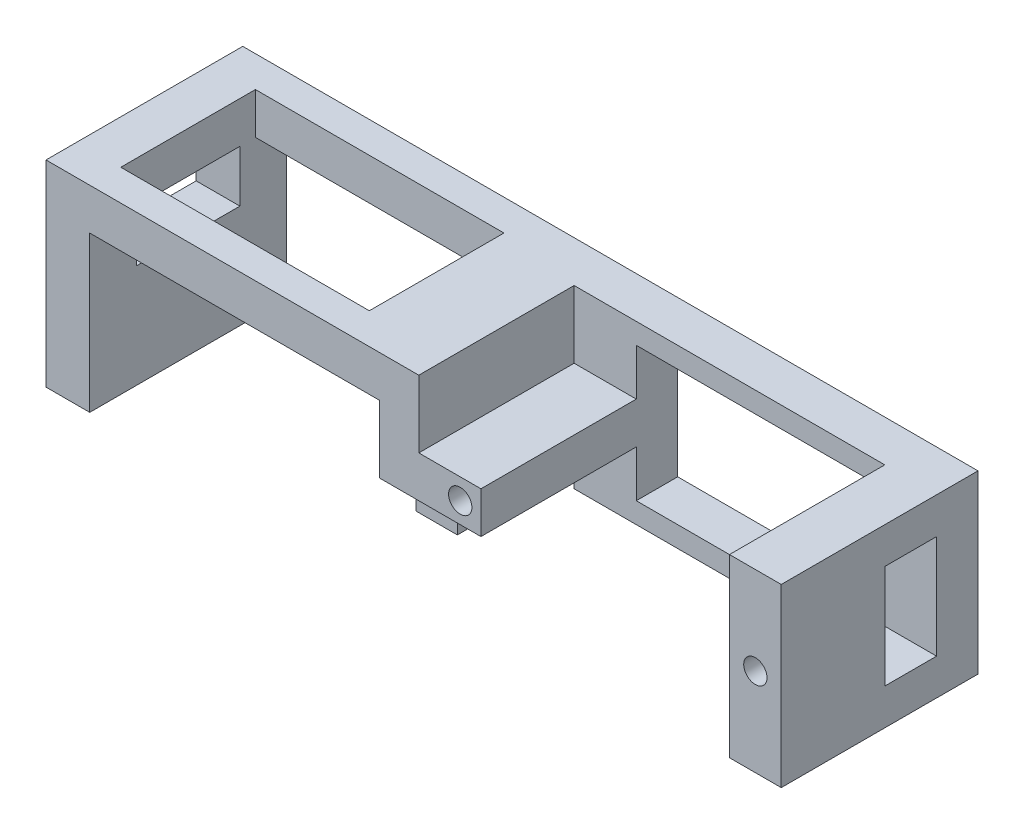
SolidWorks part; units mm, degrees
ref_plane "前基準面" through (0, 0, 0) normal (0, 0, 1) x (1, 0, 0)
ref_plane "上基準面" through (0, 0, 0) normal (0, 1, 0) x (1, 0, 0)
ref_plane "右基準面" through (0, 0, 0) normal (1, 0, 0) x (0, 0, -1)
sketch "草圖1" plane through (0, 0, 0) normal (0, 0, 1) x (1, 0, 0)
  line L0 (-21.2211, 2.8) -> (13.7789, 2.8) construction
  line L1 (-21.2211, 11.3) -> (13.7789, 11.3)
  line L2 (-21.2211, 11.3) -> (-21.2211, -5.7)
  line L3 (-21.2211, -5.7) -> (13.7789, -5.7)
  line L4 (13.7789, 11.3) -> (13.7789, -5.7)
  dimension "D1" = 35
  dimension "D2" = 8.5
extrude "填料-伸長1" add sketch "草圖1" along normal blind 4
sketch "草圖2" plane through (0, 0, 0) normal (0, 0, 1) x (1, 0, 0)
  line L0 (-21.2211, 2.8) -> (13.7789, 2.8) construction
  line L1 (-21.2211, 11.3) -> (-21.2211, -5.7) construction
  line L2 (13.7789, -5.7) -> (13.7789, 11.3) construction
  line L3 (-3.7211, 11.3) -> (-3.7211, -5.7) construction
  line L4 (13.7789, 11.3) -> (-21.2211, 11.3) construction
  line L5 (-21.2211, -5.7) -> (13.7789, -5.7) construction
  line L7 (-15.2211, 9.3) -> (8.7789, 9.3)
  line L8 (-15.2211, 9.3) -> (-15.2211, -3.7)
  line L9 (-15.2211, -3.7) -> (8.7789, -3.7)
  line L10 (8.7789, 9.3) -> (8.7789, -3.7)
  dimension "D1" = 24
  dimension "D2" = 13
  dimension "D3" = 6.5
  dimension "D4" = 5
extrude "除料-伸長1" cut sketch "草圖2" along normal blind 6
ref_plane "平面1" through (13.7789, 0, 0) normal (1, 0, 0) x (0, 0, -1)
sketch "草圖3" plane through (13.7789, 0, 0) normal (1, 0, 0) x (0, 0, -1)
  line L0 (-4, 2.8025) -> (-19, 2.8025) construction
  line L1 (-4, 11.3) -> (-19, 11.3)
  line L3 (-4, -5.6949) -> (-19, -5.6949)
  line L4 (-19, 11.3) -> (-19, -5.6949)
  line L5 (-4, 11.3) -> (-4, -5.6949)
  line L6 (-9, 7.8025) -> (-4, 7.8025)
  line L7 (-9, 7.8025) -> (-9, -2.1975)
  line L8 (-9, -2.1975) -> (-4, -2.1975)
  line L9 (-4, 7.8025) -> (-4, -2.1975)
  dimension "D1" = 15
  dimension "D2" = 5
  dimension "D3" = 10
  dimension "D4" = 5
extrude "填料-伸長2" add sketch "草圖3" against normal blind 5 contours L7 L0 L4 L3 L5 L8 | L0 L7 L6 L5 L1 L4
ref_plane "平面2" through (0, 0, 4) normal (0, 0, 1) x (1, 0, 0)
sketch "草圖5" plane through (0, 0, 4) normal (0, 0, 1) x (1, 0, 0)
  line L0 (-21.2211, 2.8) -> (-15.2211, 2.8) construction
  line L1 (-21.2211, 11.3) -> (-21.2211, -5.7) construction
  line L2 (-15.2211, -3.7) -> (-15.2211, 9.3) construction
  line L3 (-17.2211, 4.8) -> (-17.2211, 0.8) construction
  line L4 (-19.2211, 4.8) -> (-15.2211, 4.8)
  line L5 (-19.2211, 4.8) -> (-19.2211, 0.8)
  line L6 (-19.2211, 0.8) -> (-15.2211, 0.8)
  line L7 (-15.2211, 4.8) -> (-15.2211, 0.8)
  circle A0 centre (-17.2211, 2.8) radius 1.125
  dimension "D4" = 2.25
  dimension "D1" = 4
  dimension "D2" = 4
  dimension "D3" = 2
extrude "填料-伸長3" add sketch "草圖5" along normal blind 15
ref_plane "平面3" through (0, 0, 19) normal (0, 0, 1) x (1, 0, 0)
sketch "草圖6" plane through (0, 0, 19) normal (0, 0, 1) x (1, 0, 0)
  line L0 (8.7789, 2.8025) -> (13.7789, 2.8025) construction
  line L1 (8.7789, 11.3) -> (8.7789, -5.6949) construction
  line L2 (13.7789, -9.35) -> (13.7789, 9.35) construction
  line L3 (11.2789, 11.3) -> (11.2789, -5.6949) construction
  line L4 (8.7789, 11.3) -> (13.7789, 11.3) construction
  line L5 (8.7789, -5.6949) -> (13.7789, -5.6949) construction
  circle A0 centre (11.2789, 2.8025) radius 1.125
  dimension "D1" = 2.25
extrude "除料-伸長2" cut sketch "草圖6" against normal blind 15
ref_plane "平面4" through (-21.2211, 0, 0) normal (-1, 0, 0) x (0, 0, 1)
sketch "草圖7" plane through (-21.2211, 0, 0) normal (-1, 0, 0) x (0, 0, 1)
  line L6 (4, 4.8) -> (4, 0.7965)
  line L7 (4, -3.575) -> (4, 3.575) construction
  line L8 (19, 4.8) -> (4, 4.8) construction
  line L9 (4, 0.7965) -> (19, 0.8)
  line L10 (19, -2.75) -> (19, 2.75) construction
  line L11 (19, 0.8) -> (4, 0.8) construction
  line L12 (19, 0.8) -> (19, 4.8)
  line L13 (19, 4.8) -> (4, 4.8)
extrude "填料-伸長5" add sketch "草圖7" against normal blind 2
ref_plane "平面5" through (0, 3, 0) normal (0, 1, 0) x (1, 0, 0)
sketch "草圖8" plane through (0, 3, 0) normal (0, 1, 0) x (1, 0, 0)
  line L1 (-21.2211, -19) -> (-57.2211, -19)
  line L2 (-21.2211, -19) -> (-21.2211, 0)
  line L3 (-21.2211, 0) -> (-57.2211, 0)
  line L4 (-57.2211, -19) -> (-57.2211, 0)
  dimension "D1" = 19
  dimension "D2" = 36
extrude "填料-伸長6" add sketch "草圖8" along normal blind 8.3 and the other way blind 10.7
ref_plane "平面6" through (0, 11.3, 0) normal (0, 1, 0) x (1, 0, 0)
sketch "草圖9" plane through (0, 11.3, 0) normal (0, 1, 0) x (1, 0, 0)
  line L0 (-57.2211, -9.5) -> (-15.2211, -9.5) construction
  line L1 (-57.2211, 0) -> (-57.2211, -19) construction
  line L2 (-15.2211, -19) -> (-15.2211, -4) construction
  line L4 (-52.9984, -3) -> (-28.9984, -3)
  line L5 (-52.9984, -3) -> (-52.9984, -16)
  line L6 (-52.9984, -16) -> (-28.9984, -16)
  line L7 (-28.9984, -3) -> (-28.9984, -16)
  dimension "D1" = 24
  dimension "D2" = 13
  dimension "D3" = 6.5
extrude "除料-伸長3" cut sketch "草圖9" against normal blind 22
ref_plane "平面7" through (0, -7.7, 0) normal (0, -1, 0) x (-1, 0, 0)
sketch "草圖11" plane through (0, -7.7, 0) normal (0, -1, 0) x (-1, 0, 0)
  line L0 (21.2211, -9.5) -> (57.2211, -9.5) construction
  line L1 (21.2211, -19) -> (21.2211, 0) construction
  line L2 (57.2211, 0) -> (57.2211, -19) construction
  line L3 (28.9984, -16) -> (28.9984, -3) construction
  line L4 (52.9984, -3) -> (52.9984, -16) construction
  circle A0 centre (26.9984, -9.5) radius 1.125
  circle A1 centre (54.9995, -9.5) radius 1.125
  dimension "D3" = 2.25
  dimension "D4" = 2.25
  dimension "D1" = 2
  dimension "D2" = 2.0011
extrude "除料-伸長4" cut sketch "草圖11" against normal blind 15
sketch "草圖12" plane through (0, -7.7, 0) normal (0, -1, 0) x (-1, 0, 0)
  line L0 (21.2211, -9.5) -> (57.2211, -9.5) construction
  line L1 (21.2211, -19) -> (21.2211, 0) construction
  line L2 (57.2211, 0) -> (57.2211, -19) construction
  line L3 (28.9984, -7.5) -> (24.9984, -7.5)
  line L4 (28.9984, -16) -> (28.9984, -3) construction
  line L7 (24.9984, -11.5) -> (24.9984, -19)
  line L8 (57.2211, -19) -> (21.2211, -19) construction
  line L9 (24.9984, -19) -> (52.9984, -19)
  line L10 (52.9984, -19) -> (52.9984, -16)
  line L11 (52.9984, -16) -> (28.9984, -16)
  line L12 (28.9984, -16) -> (28.9984, -11.5)
  line L14 (28.9984, -3) -> (28.9984, -7.5)
  line L15 (52.9984, -3) -> (28.9984, -3)
  line L16 (52.9984, 0) -> (52.9984, -3)
  line L17 (24.9984, 0) -> (52.9984, 0)
  line L18 (24.9984, -7.5) -> (24.9984, 0)
  line L19 (28.9984, -11.5) -> (24.9984, -11.5)
  dimension "D1" = 4
  dimension "D2" = 4
extrude "除料-伸長5" cut sketch "草圖12" against normal blind 15
sketch "草圖13" plane through (0, -7.7, 0) normal (0, -1, 0) x (1, 0, 0)
  line L1 (-24.9984, 19) -> (-21.2211, 19)
  line L2 (-24.9984, 19) -> (-24.9984, 0)
  line L3 (-24.9984, 0) -> (-21.2211, 0)
  line L4 (-21.2211, 19) -> (-21.2211, 0)
extrude "除料-伸長6" cut sketch "草圖13" against normal blind 8.5
ref_plane "平面8" through (-57.2211, 0, 0) normal (-1, 0, 0) x (0, 0, 1)
sketch "草圖14" plane through (-57.2211, 0, 0) normal (-1, 0, 0) x (0, 0, 1)
  line L0 (10.45, 11.3) -> (-10.45, 11.3) construction
  line L1 (4.5, 7.3) -> (14.5, 7.3)
  line L2 (4.5, 7.3) -> (4.5, 2.3)
  line L3 (4.5, 2.3) -> (14.5, 2.3)
  line L4 (14.5, 7.3) -> (14.5, 2.3)
  line L7 (0, -7.7) -> (0, 11.3) construction
  dimension "D1" = 10
  dimension "D2" = 5
  dimension "D3" = 4
  dimension "D4" = 4.5
extrude "除料-伸長7" cut sketch "草圖14" against normal blind 10 contours L4 L3 L2 L1
